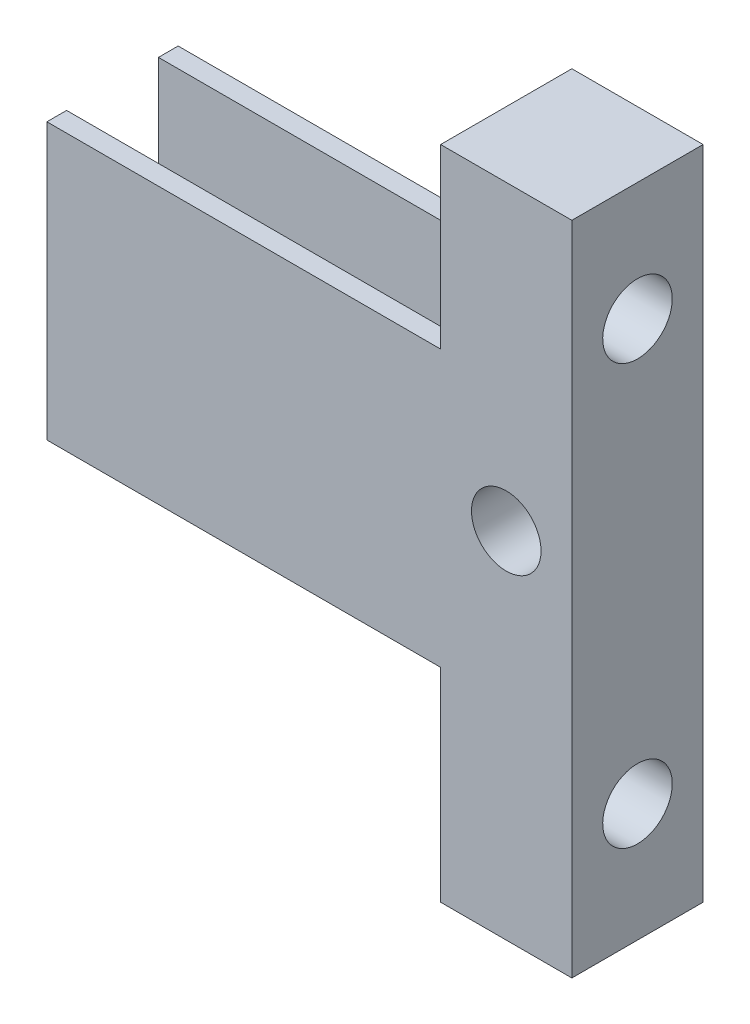
SolidWorks part; units mm, degrees
ref_plane "Front Plane" through (0, 0, 0) normal (0, 0, 1) x (1, 0, 0)
ref_plane "Top Plane" through (0, 0, 0) normal (0, 1, 0) x (1, 0, 0)
ref_plane "Right Plane" through (0, 0, 0) normal (1, 0, 0) x (0, 0, -1)
sketch "Sketch2" plane through (0, 0, 0) normal (0, 0, 1) x (1, 0, 0)
  line L8 (0, 0) -> (0, 50)
  line L9 (0, 50) -> (10, 50)
  line L10 (10, 50) -> (10, 0)
  line L11 (10, 0) -> (0, 0)
  dimension "D1" = 50
  dimension "D2" = 10
extrude "Boss-Extrude1" add sketch "Sketch2" along normal blind 10 contours L11 L8 L9 L10
sketch "Sketch6" plane through (0, 0, 10) normal (0, 0, 1) x (1, 0, 0)
  line L0 (10, 50) -> (10, 0) construction
  line L1 (10, 0) -> (0, 0) construction
  circle A0 centre (5, 27) radius 2.65
  dimension "D1" = 5.3
  dimension "D2" = 5
  dimension "D3" = 27
extrude "Cut-Extrude3" cut sketch "Sketch6" against normal through all contours A0
sketch "Sketch7" plane through (0, 0, 0) normal (-1, 0, 0) x (0, 0, 1)
  line L0 (10, 0) -> (10, 50) construction
  line L1 (10, 0) -> (0, 0) construction
  circle A0 centre (5, 41) radius 2.65
  circle A1 centre (5, 9) radius 2.65
  dimension "D3" = 5.3
  dimension "D4" = 5.3
  dimension "D5" = 9
  dimension "D1" = 32
  dimension "D2" = 5
  dimension "D6" = 5
extrude "Cut-Extrude4" cut sketch "Sketch7" against normal through all
sketch "Sketch8" plane through (0, 0, 0) normal (-1, 0, 0) x (0, 0, 1)
  line L0 (8.5, 36.5) -> (8.5, 15.5)
  line L1 (8.5, 15.5) -> (10, 15.5)
  line L2 (10, 0) -> (10, 50) construction
  line L3 (10, 15.5) -> (10, 36.5)
  line L4 (10, 36.5) -> (8.5, 36.5)
  line L5 (1.5, 36.5) -> (1.5, 15.5)
  line L6 (1.5, 15.5) -> (0, 15.5)
  line L7 (0, 0) -> (0, 50) construction
  line L8 (0, 15.5) -> (0, 36.5)
  line L9 (0, 36.5) -> (1.5, 36.5)
  line L10 (10, 50) -> (0, 50) construction
  dimension "D1" = 1.5
  dimension "D2" = 1.5
  dimension "D3" = 13.5
  dimension "D4" = 21
extrude "Boss-Extrude2" add sketch "Sketch8" along normal blind 30
